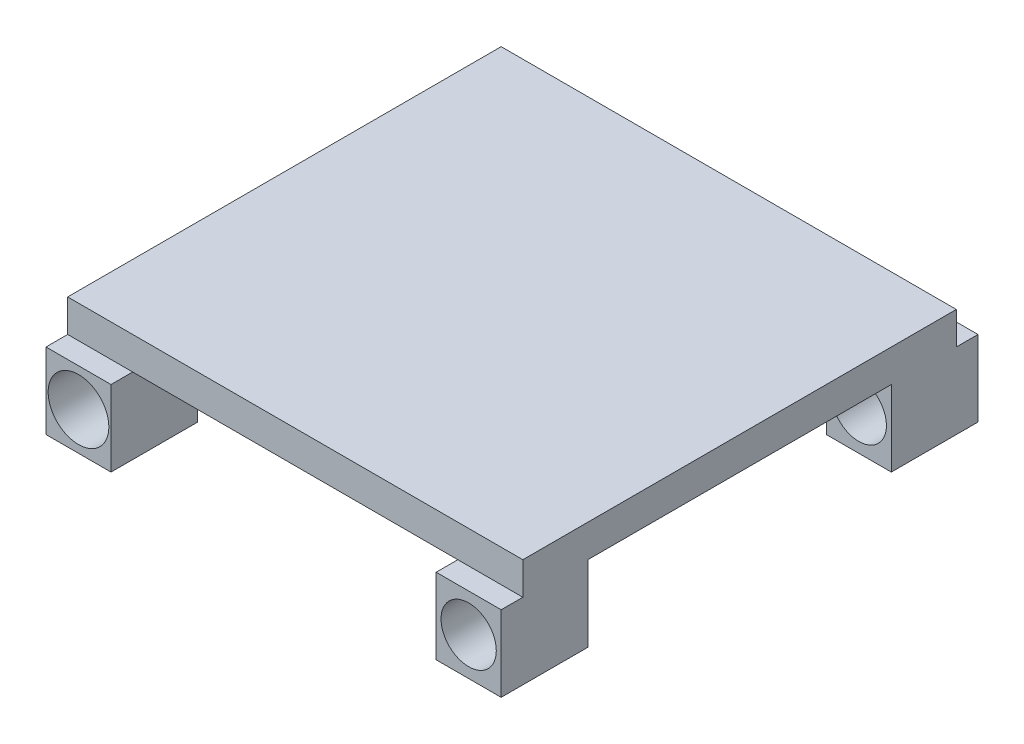
SolidWorks part; units mm, degrees
ref_plane "Ön Düzlem" through (0, 0, 0) normal (0, 0, 1) x (1, 0, 0)
ref_plane "Üst Düzlem" through (0, 0, 0) normal (0, 1, 0) x (1, 0, 0)
ref_plane "Sağ Düzlem" through (0, 0, 0) normal (1, 0, 0) x (0, 0, -1)
sketch "Çizim1" plane through (0, 0, 0) normal (0, 1, 0) x (1, 0, 0)
  line L0 (-127.8643, 75) -> (82.1357, 75)
  line L2 (-127.8643, -125) -> (82.1357, -125)
  line L3 (-127.8643, 75) -> (-127.8643, -125)
  line L4 (82.1357, -125) -> (82.1357, 75)
  point P0 (-86.739, -68.8804)
  dimension "D2" = 200
  dimension "D4" = 210
extrude "Yükseklik-Ekstrüzyon1" add sketch "Çizim1" along normal blind 15
ref_plane "Düzlem1" through (82.1357, 0, 0) normal (1, 0, 0) x (0, 0, -1)
sketch "Çizim2" plane through (82.1357, 0, 0) normal (1, 0, 0) x (0, 0, -1)
  line L0 (-135, 0) -> (-95, 0)
  line L1 (-125, 0) -> (75, 0) construction
  line L2 (-95, 0) -> (-95, -35)
  line L3 (-95, -35) -> (-135, -35)
  line L4 (-135, -35) -> (-135, 0)
  line L5 (-25, 53.591) -> (-25, -90.7521) construction
  line L6 (45, -35) -> (85, -35)
  line L7 (45, 0) -> (45, -35)
  line L8 (85, 0) -> (45, 0)
  line L9 (85, -35) -> (85, 0)
  line L11 (-125, 15) -> (-125, 0) construction
  dimension "D1" = 40
  dimension "D2" = 40
  dimension "D3" = 30
  dimension "D4" = 35
  dimension "D5" = 30
extrude "Yükseklik-Ekstrüzyon2" add sketch "Çizim2" against normal blind 30
ref_plane "Düzlem2" through (-22.8643, 0, 0) normal (1, 0, 0) x (0, 0, -1)
mirror "Aynalama1" about plane through (-22.8643, 0, 0) normal (1, 0, 0) of "Yükseklik-Ekstrüzyon2"
sketch "Çizim7" plane through (0, 0, 135) normal (0, 0, 1) x (1, 0, 0)
  line L2 (-112.8643, -45.5573) -> (-112.8643, 44.5358) construction
  line L4 (-132.5543, -20) -> (-79.0426, -20) construction
  line L5 (-127.8643, 0) -> (-127.8643, -35) construction
  line L7 (-97.8643, -35) -> (-127.8643, -35) construction
  line L8 (52.1357, 0) -> (82.1357, 0) construction
  line L9 (52.1357, 0) -> (52.1357, -35) construction
  circle A0 centre (67.1357, -17.5) radius 12.75
  circle A1 centre (-112.8643, -17.5) radius 14
  dimension "D1" = 25.5
  dimension "D2" = 28
  dimension "D3" = 15
  dimension "D4" = 17.5
  dimension "D5" = 17.5
  dimension "D6" = 15
extrude "Kes-Ekstrüzyon2" cut sketch "Çizim7" against normal blind 504
